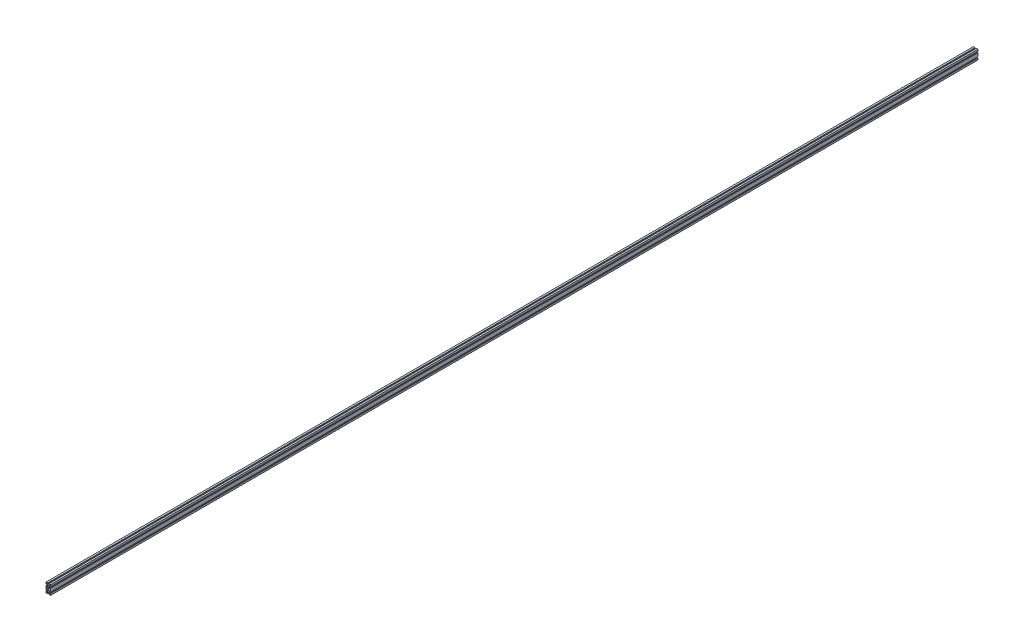
SolidWorks part; units mm, degrees
ref_plane "Front Plane" through (0, 0, 0) normal (0, 0, 1) x (1, 0, 0)
ref_plane "Top Plane" through (0, 0, 0) normal (0, 1, 0) x (1, 0, 0)
ref_plane "Right Plane" through (0, 0, 0) normal (1, 0, 0) x (0, 0, -1)
sketch "B01-6" plane through (0, 0, 0) normal (0, 0, 1) x (1, 0, 0)
  line L94 (-7.6553, -9.6031) -> (-7.2022, -9.603)
  line L95 (7.2022, -9.603) -> (7.6553, -9.6031)
  line L96 (7.6553, 9.6031) -> (7.2022, 9.603)
  line L97 (-7.2022, 9.603) -> (-7.6553, 9.6031)
  line L98 (-13, -22.2657) -> (-11.6343, -22.2657)
  line L99 (-11.6343, -7.7343) -> (-13, -7.7343)
  line L100 (-13, 7.7343) -> (-11.6343, 7.7343)
  line L101 (-11.6343, 22.2657) -> (-13, 22.2657)
  line L102 (-7.2657, 28) -> (-7.2657, 26.6343)
  line L103 (7.2657, 26.6343) -> (7.2657, 28)
  line L104 (13, 22.2657) -> (11.6343, 22.2657)
  line L105 (11.6343, 7.7343) -> (13, 7.7343)
  line L106 (13, -7.7343) -> (11.6343, -7.7343)
  line L107 (11.6343, -22.2657) -> (13, -22.2657)
  line L108 (7.2657, -28) -> (7.2657, -26.6343)
  line L109 (-7.2657, -26.6343) -> (-7.2657, -28)
  line L110 (12.9945, 6) -> (12.9945, -6)
  line L111 (12.9945, -6) -> (11.2584, -6)
  line L112 (11.2584, -6) -> (7.6553, -9.6031)
  line L113 (-7.6553, -9.6031) -> (-11.2584, -6)
  line L114 (-11.2584, -6) -> (-12.9945, -6)
  line L115 (-12.9945, -6) -> (-12.9945, 6)
  line L116 (-12.9945, 6) -> (-11.2584, 6)
  line L117 (-11.2584, 6) -> (-7.6553, 9.6031)
  line L118 (7.6553, 9.6031) -> (11.2584, 6)
  line L119 (11.2584, 6) -> (12.9945, 6)
  line L120 (-13.5, -28.5) -> (-13.5, -24)
  line L121 (-13.5, -24) -> (-9, -24)
  line L122 (-9, -24) -> (-9, -28.5)
  line L123 (-9, -28.5) -> (-13.5, -28.5)
  line L124 (-9, 24) -> (-13.5, 24)
  line L125 (-13.5, 24) -> (-13.5, 28.5)
  line L126 (-13.5, 28.5) -> (-9, 28.5)
  line L127 (-9, 28.5) -> (-9, 24)
  line L128 (9, -28.5) -> (9, -24)
  line L129 (9, -24) -> (13.5, -24)
  line L130 (13.5, -24) -> (13.5, -28.5)
  line L131 (13.5, -28.5) -> (9, -28.5)
  line L132 (9, 24) -> (9, 28.5)
  line L133 (9, 28.5) -> (13.5, 28.5)
  line L134 (13.5, 28.5) -> (13.5, 24)
  line L135 (13.5, 24) -> (9, 24)
  line L136 (15, 30) -> (15, 19)
  line L137 (4, 30) -> (15, 30)
  line L138 (4, 28) -> (4, 30)
  line L139 (7.2657, 28) -> (4, 28)
  line L140 (3.9314, 23.3) -> (7.2657, 26.6343)
  line L141 (-3.9314, 23.3) -> (3.9314, 23.3)
  line L142 (-7.2657, 26.6343) -> (-3.9314, 23.3)
  line L143 (-4, 28) -> (-7.2657, 28)
  line L144 (-4, 30) -> (-4, 28)
  line L145 (-15, 30) -> (-4, 30)
  line L146 (-15, 19) -> (-15, 30)
  line L147 (-13, 19) -> (-15, 19)
  line L148 (-13, 22.2657) -> (-13, 19)
  line L149 (-8.3, 18.9314) -> (-11.6343, 22.2657)
  line L150 (-8.3, 11.0686) -> (-8.3, 18.9314)
  line L151 (-11.6343, 7.7343) -> (-8.3, 11.0686)
  line L152 (-13, 11) -> (-13, 7.7343)
  line L153 (-15, 11) -> (-13, 11)
  line L154 (-15, -11) -> (-15, 11)
  line L155 (-13, -11) -> (-15, -11)
  line L156 (-13, -7.7343) -> (-13, -11)
  line L157 (-8.3, -11.0686) -> (-11.6343, -7.7343)
  line L158 (-8.3, -18.9314) -> (-8.3, -11.0686)
  line L159 (-11.6343, -22.2657) -> (-8.3, -18.9314)
  line L160 (-13, -19) -> (-13, -22.2657)
  line L161 (-15, -19) -> (-13, -19)
  line L162 (-15, -30) -> (-15, -19)
  line L163 (-4, -30) -> (-15, -30)
  line L164 (-4, -28) -> (-4, -30)
  line L165 (-7.2657, -28) -> (-4, -28)
  line L166 (-3.9314, -23.3) -> (-7.2657, -26.6343)
  line L167 (3.9314, -23.3) -> (-3.9314, -23.3)
  line L168 (7.2657, -26.6343) -> (3.9314, -23.3)
  line L169 (4, -28) -> (7.2657, -28)
  line L170 (4, -30) -> (4, -28)
  line L171 (15, -30) -> (4, -30)
  line L172 (15, -19) -> (15, -30)
  line L173 (13, -19) -> (15, -19)
  line L174 (13, -22.2657) -> (13, -19)
  line L175 (8.3, -18.9314) -> (11.6343, -22.2657)
  line L176 (8.3, -11.0686) -> (8.3, -18.9314)
  line L177 (11.6343, -7.7343) -> (8.3, -11.0686)
  line L178 (13, -11) -> (13, -7.7343)
  line L179 (15, -11) -> (13, -11)
  line L180 (15, 11) -> (15, -11)
  line L181 (13, 11) -> (15, 11)
  line L182 (13, 7.7343) -> (13, 11)
  line L183 (8.3, 11.0686) -> (11.6343, 7.7343)
  line L184 (8.3, 18.9314) -> (8.3, 11.0686)
  line L185 (11.6343, 22.2657) -> (8.3, 18.9314)
  line L186 (13, 19) -> (13, 22.2657)
  line L187 (15, 19) -> (13, 19)
  arc A4 (7.2022, -9.603) -> (-7.2022, -9.603) centre (0, -15) ccw
  arc A5 (-7.2022, 9.603) -> (7.2022, 9.603) centre (0, 15) ccw
  circle A6 centre (0, -15) radius 6.05
  circle A7 centre (0, 15) radius 6.05
extrude "Extrude1" add sketch "B01-6" against normal blind 6000
